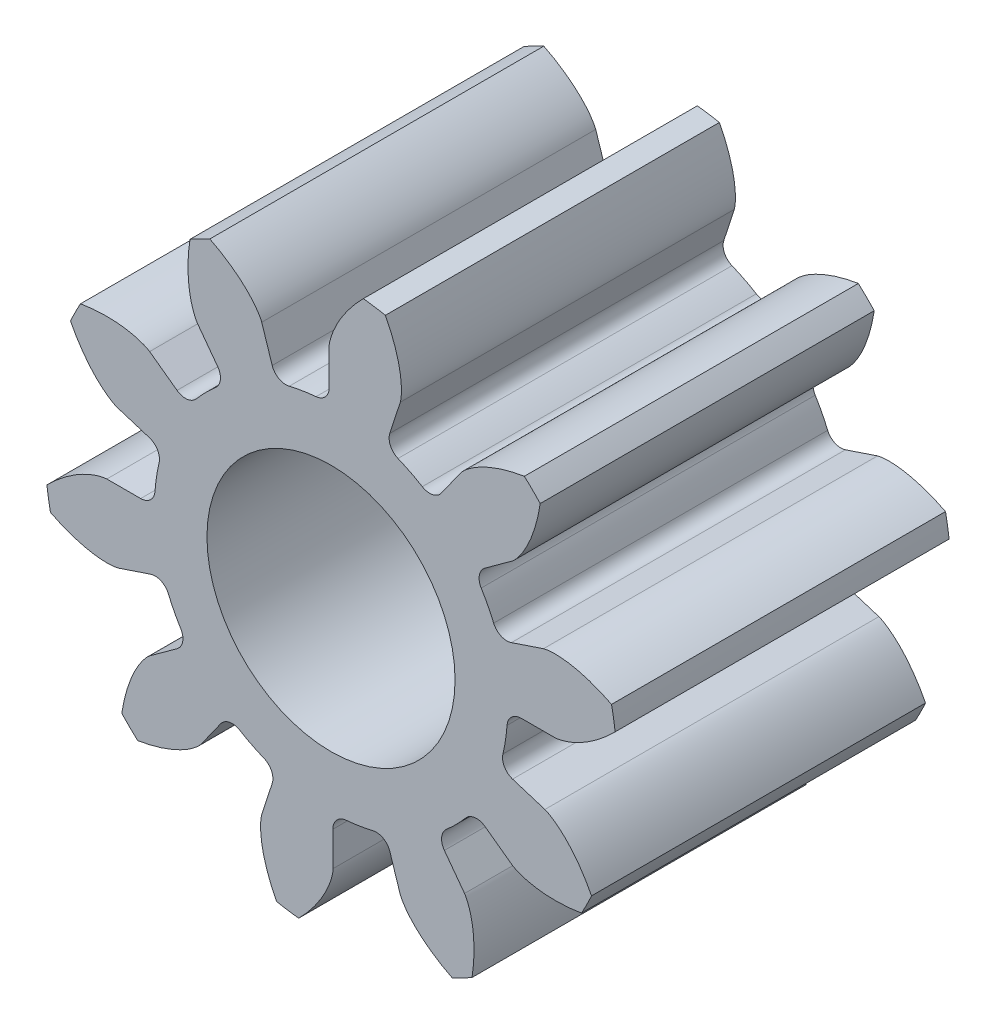
SolidWorks part; units mm, degrees
other "Annotazione1"
sketch "Schizzo1" plane through (5.4895, -5.4895, 0) normal (0.8276, -0.4919, -0.2704) x (-0.1174, 0.3193, -0.9403)
sketch "Schizzo2" plane through (5.4895, -5.4895, 0) normal (0.8276, -0.4919, -0.2704) x (-0.1174, 0.3193, -0.9403)
sketch "Schizzo3" plane through (5.6481, -5.6667, 0) normal (0.8276, -0.4919, -0.2704) x (-0.1174, 0.3193, -0.9403)
material "Acrilico (impatto medio-alto)"
ref_plane "Front Plane" through (0, 0, 0) normal (0, 0, 1) x (1, 0, 0)
ref_plane "Top Plane" through (0, 0, 0) normal (0, 1, 0) x (1, 0, 0)
ref_plane "Right Plane" through (0, 0, 0) normal (1, 0, 0) x (0, 0, -1)
sketch "Sketch1" plane through (0, 0, 0) normal (0, 0, 1) x (1, 0, 0)
  line L0 (4.6985, 0) -> (3.7, 0)
  line L1 (5.9215, 0.9677) -> (-5.9215, -0.9677)
  line L2 (0, 0) -> (4.9994, 0.0745) construction
  circle A0 centre (0, 0) radius 4.6985 construction
  circle A1 centre (0, 0) radius 6
  circle A2 centre (0, 0) radius 3.7
  circle A3 centre (0, 0) radius 5 construction
  spline S0 degree 4 poles (4.6985, 0) (4.7019, 0.0001) (4.7117, 0.0005) (4.73, 0.0022) (4.7599, 0.0063) (4.7977, 0.0133) (4.8462, 0.0246) (4.9027, 0.0405) (4.9642, 0.0609) (5.0303, 0.086) (5.0954, 0.1137) (5.1594, 0.1437) (5.2224, 0.1758) (5.2977, 0.2172) (5.3864, 0.2702) (5.4878, 0.3372) (5.5997, 0.4188) (5.7102, 0.508) (5.8161, 0.6006) (5.9193, 0.6994) (6.0166, 0.7988) (6.1136, 0.9071) (6.2011, 1.0098) (6.2943, 1.1303) (6.3682, 1.2291) (6.4603, 1.365) (6.5131, 1.4469) (6.573, 1.5445) (6.5986, 1.5888) (6.6144, 1.6161) knots 0 0 0 0 0 0.005377 0.015084 0.028532 0.04661 0.064855 0.092111 0.119476 0.146842 0.174209 0.201575 0.228941 0.256307 0.307035 0.361767 0.4165 0.471232 0.525964 0.580697 0.635429 0.690161 0.744894 0.799626 0.854358 0.909091 0.954545 1 1 1 1 1 construction
  spline S1 degree 4 poles (4.6985, 0) (4.7019, 0.0001) (4.7117, 0.0005) (4.73, 0.0022) (4.7599, 0.0063) (4.7977, 0.0133) (4.8462, 0.0246) (4.9027, 0.0405) (4.9642, 0.0609) (5.0303, 0.086) (5.0954, 0.1137) (5.1594, 0.1437) (5.2224, 0.1758) (5.2977, 0.2172) (5.3864, 0.2702) (5.4878, 0.3372) (5.5997, 0.4188) (5.7102, 0.508) (5.8161, 0.6006) (5.9193, 0.6994) (6.0166, 0.7988) (6.1136, 0.9071) (6.2011, 1.0098) (6.2943, 1.1303) (6.3682, 1.2291) (6.4403, 1.3356) (6.4748, 1.388) (6.4922, 1.415) knots 0 0 0 0 0 0.005377 0.015084 0.028532 0.04661 0.064855 0.092111 0.119476 0.146842 0.174209 0.201575 0.228941 0.256307 0.307035 0.361767 0.4165 0.471232 0.525964 0.580697 0.635429 0.690161 0.744894 0.799626 0.854358 0.909091 0.909091 0.909091 0.909091 0.909091
  dimension "D1" = 9.3969
  dimension "D2" = 12
  dimension "D3" = 7.4
  dimension "D5" = 10
  dimension "D4" = 8.427
extrude "Boss-Extrude3" add sketch "Sketch1" along normal blind 7 contours L1 A2 | A2 L1 | L0 S1 A1 L1 A2
mirror "Mirror2" about plane through (0, 0, 7) normal (0.1613, -0.9869, 0) of "Boss-Extrude3"
fillet "Fillet1" radius 0.3 2 edges at (3.5075, 1.1778, 3.5) (3.7, 0, 3.5)
pattern_circular "CirPattern8" count 10 over 360 about axis through (0, 0, 7) along (0, 0, -1) of "Boss-Extrude3", "Mirror2", "Fillet1"
sketch "Sketch3" plane through (0, 0, 7) normal (0, 0, 1) x (1, 0, 0)
  circle A0 centre (0, 0) radius 2.6
  dimension "D1" = 5.2
extrude "Cut-Extrude2" cut sketch "Sketch3" against normal through all
equation "\"d\"= 10mm'Pitch diameter"
equation "\"N\" = 10'Number of teeth"
equation "\"bl\"= 0.1mm'Backlash"
equation "\"pa\"= 20gradi'Pressure angle (deg)"
equation "\"pc\"= ( 3.1415 * \"d\" ) / \"N\"\t'Circular pitch"
equation "\"m\"= \"d\" / \"N\"'module"
equation "\"P\"= \"N\" / \"d\"\t\t\t'Diametral pitch"
equation "\"a\"= 1 / \"P\"'Addendum distance"
equation "\"b\"= 1.3 / \"P\"'Dedendum distance"
equation "\"rb\"= (\"d\"/2)*cos(\"pa\")\t\t'base circle radius"
equation "\"cp\"= 3.1415/\"P\"\t\t'Circular pitch"
equation "\"t\"= ( \"cp\" / 2 ) - \"bl\"'tooth tickness"
equation "\"c\"=\"b\"-\"a\"\t\t\t'Clearance"
equation "\"facewidth\"= 7mm'face width"
equation "\"rbd\"= \"rb\" * 2'base circle diameter"
equation "\"D1@Sketch1\"=\"rbd\""
equation "\"D2@Sketch1\"= \"d\" + (\"a\" * 2)"
equation "\"D3@Sketch1\" = \"ded\""
equation "\"D4@Sketch1\"= ((\"t\" /2) / (\"d\"/2)) * (180/3.1415)"
equation "\"D1@Boss-Extrude3\"=\"facewidth\""
equation "\"D1@Fillet1\"=\"c\""
equation "\"D1@CirPattern8\"=\"N\""
equation "\"D5@Sketch1\"=\"d\""
equation "\"ded1\"= \"d\" - 2 * ( ( ( \"d\" / 2 ) - \"rb\" ) + ( 0.5 * ( 1.25 / \"P\" ) ) )"
equation "\"ded2\"= \"d\" - ( \"b\" * 2 )"
equation "\"ded\"= IIF ( \"rb\" < ( \"ded2\" / 2 ) , \"ded1\" , \"ded2\" )"
equation "\"shaftdia\"= 5.2mm"
equation "\"D1@Sketch3\"=\"shaftdia\""
